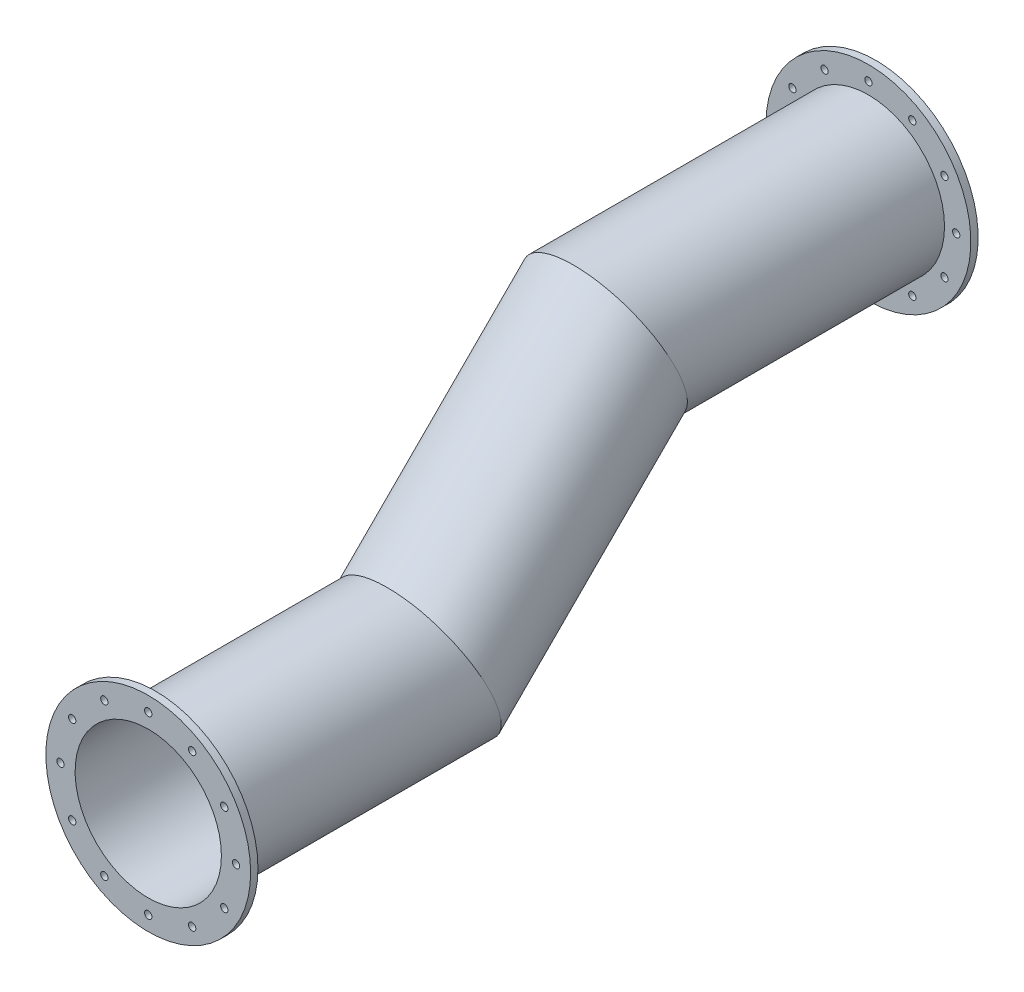
SolidWorks part; units mm, degrees
ref_plane "Front Plane" through (0, 0, 0) normal (0, 0, 1) x (1, 0, 0)
ref_plane "Top Plane" through (0, 0, 0) normal (0, 1, 0) x (1, 0, 0)
ref_plane "Right Plane" through (0, 0, 0) normal (1, 0, 0) x (0, 0, -1)
sketch "Sketch2" plane through (0, 0, 0) normal (0, 0, 1) x (1, 0, 0)
  circle A0 centre (0, 0) radius 50
  dimension "D1" = 100
sketch "Sketch3" plane through (0, 0, 0) normal (1, 0, 0) x (0, 0, -1)
  line L0 (0, 0) -> (180, 0)
  line L1 (180, 0) -> (307.2792, 127.2792)
  line L2 (307.2792, 127.2792) -> (487.2792, 127.2792)
  dimension "D1" = 45
  dimension "D2" = 180
sweep "Sweep-Thin1" add profiles "Sketch2" path "Sketch3" parameters "D1"=2
sketch "Sketch4" plane through (0, 0, 0) normal (0, 0, 1) x (1, 0, 0)
  circle A0 centre (0, 0) radius 50 construction
  circle A1 centre (0, 0) radius 50
  circle A2 centre (0, 0) radius 70
  circle A3 centre (0, -60) radius 2.5
  circle A4 centre (-30, -51.9615) radius 2.5
  circle A5 centre (-51.9615, -30) radius 2.5
  circle A6 centre (-60, 0) radius 2.5
  circle A7 centre (-51.9615, 30) radius 2.5
  circle A8 centre (-30, 51.9615) radius 2.5
  circle A9 centre (0, 60) radius 2.5
  circle A10 centre (30, 51.9615) radius 2.5
  circle A11 centre (51.9615, 30) radius 2.5
  circle A12 centre (60, 0) radius 2.5
  circle A13 centre (51.9615, -30) radius 2.5
  circle A14 centre (30, -51.9615) radius 2.5
  point P5 (0, 0)
  point P31 (0, 0)
  dimension "data" = 140
  dimension "D3" = 5
  dimension "D2" = 60
  dimension "D4" = 12
extrude "Boss-Extrude1" add sketch "Sketch4" along normal blind 5
sketch "Sketch5" plane through (0, 0, -487.2792) normal (0, 0, -1) x (-1, 0, 0)
  circle A0 centre (0, 127.2792) radius 50 construction
  circle A1 centre (0, 127.2792) radius 50
  circle A2 centre (0, 127.2792) radius 70
  circle A3 centre (0, 67.2792) radius 2.5
  circle A4 centre (-30, 75.3177) radius 2.5
  circle A5 centre (-51.9615, 97.2792) radius 2.5
  circle A6 centre (-60, 127.2792) radius 2.5
  circle A7 centre (-51.9615, 157.2792) radius 2.5
  circle A8 centre (-30, 179.2407) radius 2.5
  circle A9 centre (0, 187.2792) radius 2.5
  circle A10 centre (30, 179.2407) radius 2.5
  circle A11 centre (51.9615, 157.2792) radius 2.5
  circle A12 centre (60, 127.2792) radius 2.5
  circle A13 centre (51.9615, 97.2792) radius 2.5
  circle A14 centre (30, 75.3177) radius 2.5
  point P30 (0, 127.2792)
  dimension "D1" = 140
  dimension "D2" = 5
  dimension "D3" = 60
  dimension "D4" = 12
extrude "Boss-Extrude2" add sketch "Sketch5" along normal blind 5
